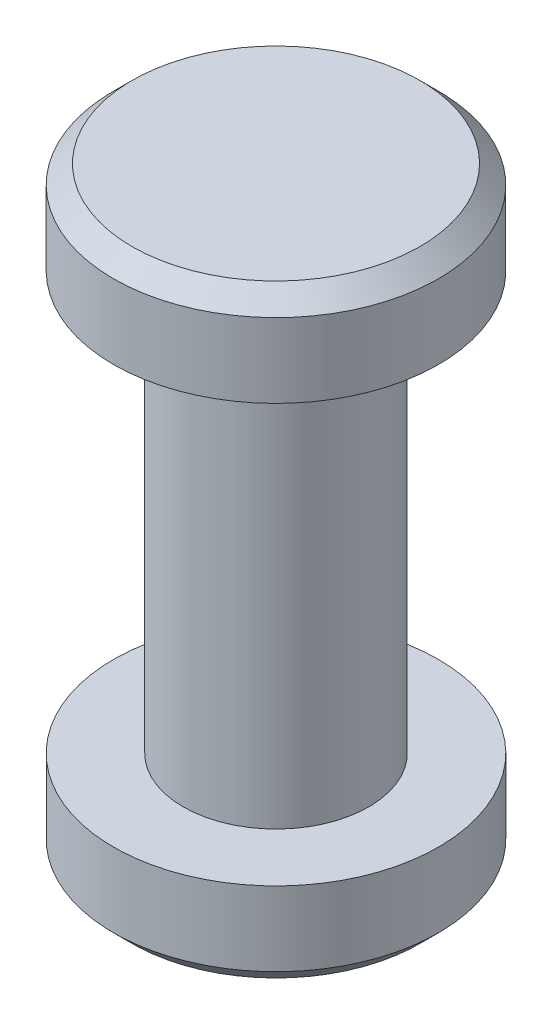
SolidWorks part; units mm, degrees
ref_plane "Front Plane" through (0, 0, 0) normal (0, 0, 1) x (1, 0, 0)
ref_plane "Top Plane" through (0, 0, 0) normal (0, 1, 0) x (1, 0, 0)
ref_plane "Right Plane" through (0, 0, 0) normal (1, 0, 0) x (0, 0, -1)
sketch "Sketch1" plane through (0, 0, 0) normal (0, 1, 0) x (1, 0, 0)
  circle A0 centre (0, 0) radius 1
  dimension "D1" = 2
extrude "Boss-Extrude1" add sketch "Sketch1" along normal blind 4.5
sketch "Sketch2" plane through (0, 4.5, 0) normal (0, 1, 0) x (1, 0, 0)
  circle A0 centre (0, 0) radius 1.75
  dimension "D1" = 3.5
extrude "Boss-Extrude2" add sketch "Sketch2" along normal blind 1
chamfer "Chamfer1" distance 0.2 angle 45 1 edges at (0, 5.5, 1.75)
sketch "Sketch3" plane through (0, 0, 0) normal (0, -1, 0) x (1, 0, 0)
  circle A0 centre (0, 0) radius 1.75
  dimension "D1" = 3.5
extrude "Boss-Extrude3" add sketch "Sketch3" along normal blind 1
chamfer "Chamfer2" distance 0.2 angle 45 1 edges at (0, -1, -1.75)
